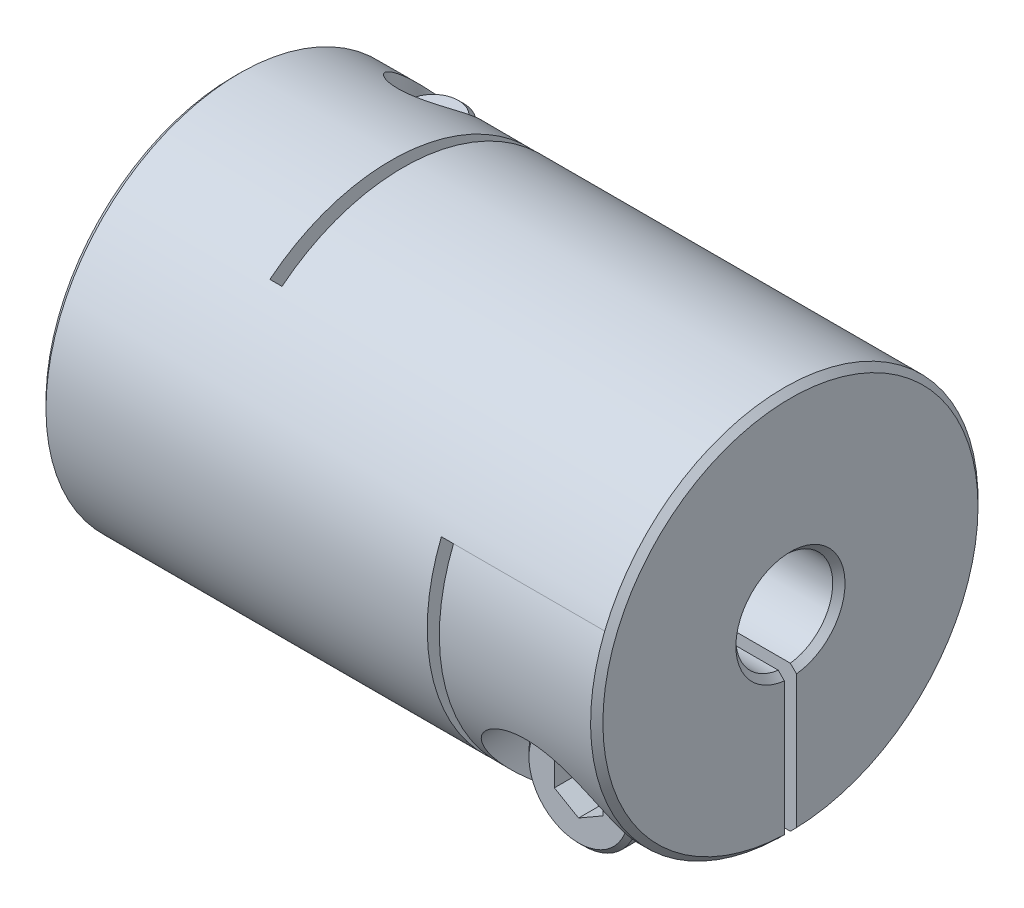
SolidWorks part; units mm, degrees
ref_plane "Front Plane" through (0, 0, 0) normal (0, 0, 1) x (1, 0, 0)
ref_plane "Top Plane" through (0, 0, 0) normal (0, 1, 0) x (1, 0, 0)
ref_plane "Right Plane" through (0, 0, 0) normal (1, 0, 0) x (0, 0, -1)
sketch "Sketch1" plane through (0, 0, 0) normal (1, 0, 0) x (0, 0, -1)
  circle A0 centre (0, 0) radius 8
  dimension "dim D" = 16
extrude "Boss-Extrude1" add sketch "Sketch1" along normal mid plane 23
sketch "Sketch2" plane through (11.5, 0, 0) normal (1, 0, 0) x (0, 0, -1)
  circle A0 centre (0, 0) radius 2
  dimension "dim D1" = 4
extrude "Cut-Extrude1" cut sketch "Sketch2" against normal through all
chamfer "Chamfer1" distance 0.254 angle 45 4 edges at (-11.5, 0, -2) (-11.5, 0, -8) (11.5, 0, -8) (11.5, 0, -2)
ref_plane "Plane2" through (0, -8, 0) normal (0, -1, 0) x (1, 0, 0)
ref_plane "L1" through (-8.25, 0, 0) normal (-1, 0, 0) x (0, 0, 1)
sketch "Sketch4" plane through (0, -8, 0) normal (0, -1, 0) x (1, 0, 0)
  line L0 (-11.246, -8) -> (11.246, -8) construction
  line L1 (-5, -8) -> (-4.5, -8)
  line L2 (-5, -8) -> (-5, 5)
  line L3 (-5, 5) -> (-4.5, 5)
  line L4 (-4.5, -8) -> (-4.5, 5)
  line L5 (-5, 2) -> (-5, 8) construction
  line L6 (11.246, 2) -> (-11.246, 2) construction
  line L7 (11.246, 8) -> (-11.246, 8) construction
  line L10 (-5, 5) -> (-11.5, 5) construction
  line L11 (-11.5, 7.746) -> (-11.5, -7.746) construction
  line L12 (-8.25, 10.2256) -> (-8.25, -10.2256) construction
  point P16 (-8.25, 5)
  dimension "D1" = 0.5
extrude "Cut-Extrude2" cut sketch "Sketch4" against normal through all
ref_plane "Plane4" through (0, 0, -8) normal (0, 0, -1) x (-1, 0, 0)
sketch "Sketch7" plane through (0, 0, -8) normal (0, 0, -1) x (-1, 0, 0)
  line L1 (-4.5, -8) -> (-5, -8)
  line L2 (-5, -8) -> (-5, 3)
  line L3 (-5, 3) -> (-4.5, 3)
  line L4 (-4.5, -8) -> (-4.5, 3)
  line L5 (11.5, 8.6487) -> (8.25, 8.6487) construction
  line L7 (-10.505, -8) -> (10.505, -8) construction
  line L8 (-11.246, -2) -> (4.5, -2) construction
  line L9 (11.5, -7.746) -> (11.5, 7.746) construction
  line L10 (-11.246, -2) -> (4.5, -2) construction
  line L11 (4.5, 6.245) -> (5, 6.245) construction
  line L12 (-5, 3) -> (-5, -8) construction
  line L14 (-11.246, -2) -> (4.5, -2) construction
  line L16 (-11.246, -2) -> (4.5, -2) construction
  line L17 (5, -8) -> (11.246, -8) construction
  line L18 (8.25, -10.2256) -> (8.25, 10.2256) construction
  line L19 (-11.246, -8) -> (-11.246, 8) construction
  line L20 (-11.5, 3) -> (-8.25, 3) construction
  line L21 (-11.5, 7.746) -> (-11.5, -7.746) construction
  line L22 (-8.25, 3) -> (-5, 3) construction
  line L23 (-11.246, -8) -> (-11.246, 8) construction
  line L24 (-11.246, -2) -> (-11.246, 8) construction
  line L25 (-11.246, -2) -> (4.5, -2) construction
  point P23 (-5, 3)
  point P33 (-11.246, 3)
extrude "Cut-Extrude3" cut sketch "Sketch7" against normal through all
sketch "Sketch8" plane through (0, 0, 0) normal (0, 1, 0) x (1, 0, 0)
  line L0 (-5, -5) -> (-5, 8) construction
  line L1 (-11.5, 8) -> (-5, 8)
  line L2 (-11.5, 8) -> (-11.5, 0)
  line L3 (-11.5, 0) -> (-5, 0)
  line L4 (-5, 8) -> (-5, 0)
  line L5 (10.505, 8) -> (-10.505, 8) construction
  line L6 (-11.5, 7.746) -> (-11.5, -7.746) construction
extrude "Cut-Extrude5" cut sketch "Sketch8" against normal mid plane 0.5
sketch "Sketch13" plane through (0, 0, 0) normal (0, 0, 1) x (1, 0, 0)
  line L0 (11.5, -7.746) -> (11.5, 7.746) construction
  line L1 (5, -8) -> (11.5, -8)
  line L2 (5, -8) -> (5, 0)
  line L3 (5, 0) -> (11.5, 0)
  line L4 (11.5, -8) -> (11.5, 0)
extrude "Cut-Extrude6" cut sketch "Sketch13" against normal mid plane 0.5
hole_wizard "CBORE for M2.5 SHCS1" positions "Sketch12" profile "Sketch11" counterbore size "M2.5" standard "Ansi Metric" end condition through all
sketch "Sketch12" plane through (0, -8, 0) normal (0, -1, 0) x (1, 0, 0)
  line L0 (-8.25, 10.2256) -> (-8.25, -10.2256) construction
  line L1 (-5, -1.9843) -> (-5, -7.9961) construction
  line L2 (-5, -1.9843) -> (-5, -7.9961)
  line L3 (-5, -4.9902) -> (-8.25, -4.9902) construction
  point P0 (-8.25, -4.9902)
sketch "Sketch11" plane through (-8.25, -8, -4.9902) normal (1, 0, 0) x (0, 0, -1)
  line L0 (0, 0) -> (0, 16)
  line L1 (0, 16) -> (1.45, 16)
  line L3 (1.45, 16) -> (1.45, 5)
  line L4 (1.45, 5) -> (2.75, 5)
  line L5 (2.75, 5) -> (2.75, 0)
  line L7 (2.75, 0) -> (0, 0)
  line L11 (0, -6.35) -> (0, 107.95) construction
  dimension "Thru Hole Dia." = 2.9
  dimension "Thru Hole Depth" = 16
  dimension "C'Bore Dia." = 5.5
  dimension "C'Bore Depth" = 5
ref_plane "Plane5" through (0, 0, 8) normal (0, 0, 1) x (1, 0, 0)
hole_wizard "CBORE for M2.5 SHCS2" positions "Sketch15" profile "Sketch14" counterbore size "M2.5" standard "Ansi Metric" end condition through all
sketch "Sketch15" plane through (0, 0, 8) normal (0, 0, 1) x (1, 0, 0)
  line L0 (-11, -3) -> (-5.5, -3) construction
  line L1 (-11, -3) -> (-5.5, -3)
  line L5 (0, 0) -> (0, 8) construction
  line L6 (-5, 8) -> (-11.246, 8) construction
  line L8 (11, -3) -> (5.5, -3)
  line L9 (8.25, -3) -> (8.25, -4.9902) construction
  line L11 (8.25, -7.9961) -> (8.25, -1.9843) construction
  line L12 (11.246, -7.9961) -> (5, -7.9961) construction
  line L13 (5, -1.9843) -> (11.246, -1.9843) construction
  point P0 (8.25, -4.9902)
sketch "Sketch14" plane through (8.25, -4.9902, 8) normal (1, 0, 0) x (0, -1, 0)
  line L0 (0, 0) -> (0, 16)
  line L1 (0, 16) -> (1.45, 16)
  line L3 (1.45, 16) -> (1.45, 5)
  line L4 (1.45, 5) -> (2.75, 5)
  line L5 (2.75, 5) -> (2.75, 0)
  line L7 (2.75, 0) -> (0, 0)
  line L11 (0, -6.35) -> (0, 107.95) construction
  dimension "Thru Hole Dia." = 2.9
  dimension "Thru Hole Depth" = 16
  dimension "C'Bore Dia." = 5.5
  dimension "C'Bore Depth" = 5
sketch "Sketch16" plane through (0, 0, 3) normal (0, 0, 1) x (1, 0, 0)
  circle A0 centre (8.25, -4.9902) radius 2.25
  dimension "screw dia" = 4.5
extrude "Boss-Extrude2" add sketch "Sketch16" along normal blind 2.5 separate body
sketch "Sketch17" plane through (0, 0, 3) normal (0, 0, -1) x (-1, 0, 0)
  circle A0 centre (-8.25, -4.9902) radius 1.25
  dimension "D1" = 2.5
extrude "Boss-Extrude3" add sketch "Sketch17" along normal blind 8.5
chamfer "Chamfer2" distance 0.2 angle 45 3 edges at (7, -4.9902, -5.5) (10.5, -4.9902, 3) (10.5, -4.9902, 5.5)
sketch "Sketch18" plane through (0, 0, 5.5) normal (0, 0, 1) x (1, 0, 0)
  line L1 (8.25, -6.1449) -> (9.25, -5.5676)
  line L2 (9.25, -5.5676) -> (9.25, -4.4129)
  line L3 (9.25, -4.4129) -> (8.25, -3.8355)
  line L4 (8.25, -3.8355) -> (7.25, -4.4129)
  line L5 (7.25, -4.4129) -> (7.25, -5.5676)
  line L6 (7.25, -5.5676) -> (8.25, -6.1449)
  circle A0 centre (8.25, -4.9902) radius 1 construction
  dimension "hex" = 2
extrude "Cut-Extrude7" cut sketch "Sketch18" against normal blind 1.5
mirror "Mirror1" about plane through (0, 0, 0) normal (1, 0, 0) of bodies 121
pattern_circular "CirPattern1" count 2 every 90 about axis through (0, 0, 0) along (1, 0, 0) of bodies 122
delete or keep bodies "Body-Delete1" type delete bodies bodies 122
